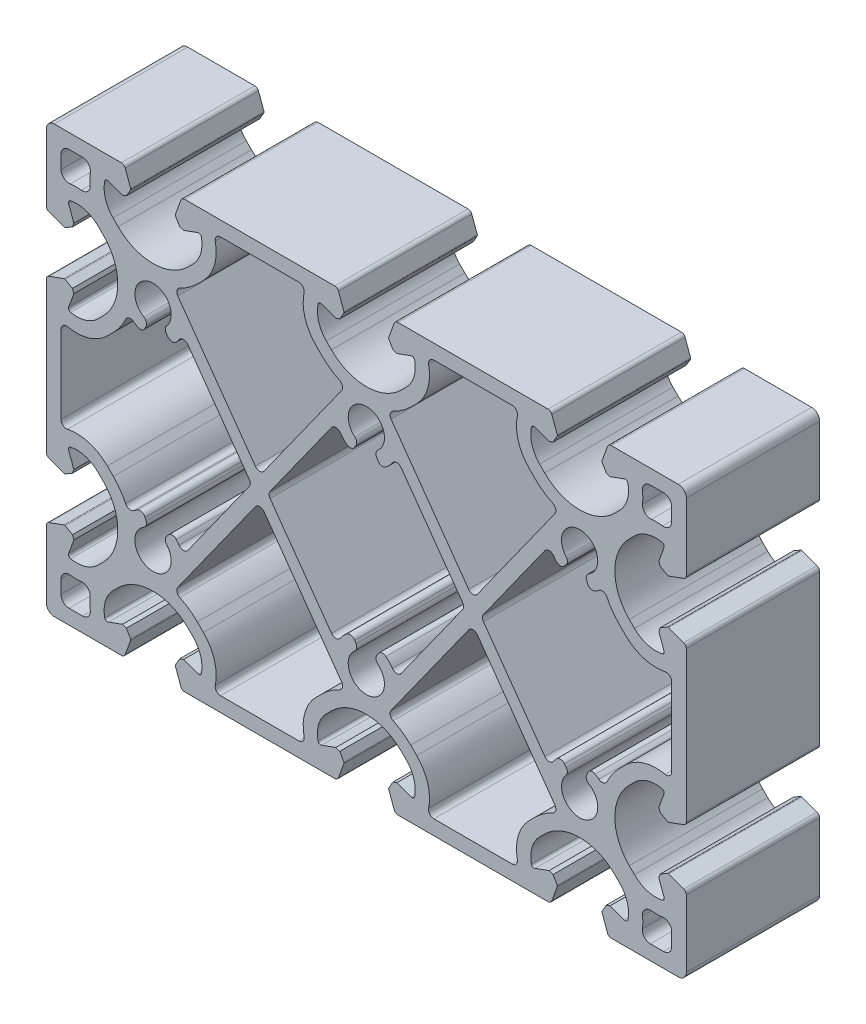
SolidWorks part; units mm, degrees
material "6005-T5"
ref_plane "Front" through (0, 0, 0) normal (0, 0, 1) x (1, 0, 0)
ref_plane "Top" through (0, 0, 0) normal (0, 1, 0) x (1, 0, 0)
ref_plane "Right" through (0, 0, 0) normal (1, 0, 0) x (0, 0, -1)
sketch "Sk Main Extrusion" plane through (0, 0, 0) normal (0, 0, 1) x (1, 0, 0)
  line L30 (-57.25, 35.75) -> (-57.25, 33.2481)
  line L31 (-53.2481, 37.25) -> (-55.75, 37.25)
  line L32 (-30.5557, 28.5773) -> (-31.6915, 27.4415)
  line L33 (-35.3543, 23.6467) -> (-20.8137, 3.2898)
  line L34 (-19.1863, 3.2898) -> (-4.6457, 23.6467)
  line L35 (-8.3085, 27.4415) -> (-9.4443, 28.5773)
  line L36 (-12.653, 37.25) -> (-27.347, 37.25)
  line L37 (-1.934, 16.1059) -> (-2.1871, 15.6675)
  line L38 (-6.5225, 16.7181) -> (-18.0487, 0.5812)
  line L39 (-18.0487, -0.5812) -> (-6.5225, -16.7181)
  line L40 (-2.1871, -15.6675) -> (-1.934, -16.1059)
  line L41 (1.934, -16.1059) -> (2.1871, -15.6675)
  line L42 (6.5225, -16.7181) -> (18.0487, -0.5812)
  line L43 (18.0487, 0.5812) -> (6.5225, 16.7181)
  line L44 (2.1871, 15.6675) -> (1.934, 16.1059)
  line L45 (9.4443, 28.5773) -> (8.3085, 27.4415)
  line L46 (4.6457, 23.6467) -> (19.1863, 3.2898)
  line L47 (20.8137, 3.2898) -> (35.3543, 23.6467)
  line L48 (31.6915, 27.4415) -> (30.5557, 28.5773)
  line L49 (27.347, 37.25) -> (12.653, 37.25)
  line L50 (37.4767, 16.4592) -> (37.1577, 16.0661)
  line L51 (33.4775, 16.7181) -> (21.9513, 0.5812)
  line L52 (21.9513, -0.5812) -> (33.4775, -16.7181)
  line L53 (37.1577, -16.0661) -> (37.4767, -16.4592)
  line L54 (41.2964, -15.8498) -> (41.4773, -15.377)
  line L55 (47.4415, -11.6915) -> (48.5773, -10.5557)
  line L56 (57.25, -7.347) -> (57.25, 7.347)
  line L57 (48.5773, 10.5557) -> (47.4415, 11.6915)
  line L58 (41.4773, 15.377) -> (41.2964, 15.8498)
  line L59 (57.25, 33.2481) -> (57.25, 35.75)
  line L60 (55.75, 37.25) -> (53.2481, 37.25)
  line L61 (-37.1577, 16.0661) -> (-37.4767, 16.4592)
  line L62 (-41.2964, 15.8498) -> (-41.4773, 15.377)
  line L63 (-47.4415, 11.6915) -> (-48.5773, 10.5557)
  line L64 (-57.25, 7.347) -> (-57.25, -7.347)
  line L65 (-48.5773, -10.5557) -> (-47.4415, -11.6915)
  line L66 (-41.4773, -15.377) -> (-41.2964, -15.8498)
  line L67 (-37.4767, -16.4592) -> (-37.1577, -16.0661)
  line L68 (-33.4775, -16.7181) -> (-21.9513, -0.5812)
  line L69 (-21.9513, 0.5812) -> (-33.4775, 16.7181)
  line L70 (-57.25, -33.2481) -> (-57.25, -35.75)
  line L71 (-55.75, -37.25) -> (-53.2481, -37.25)
  line L72 (-4.6457, -23.6467) -> (-19.1863, -3.2898)
  line L73 (-20.8137, -3.2898) -> (-35.3543, -23.6467)
  line L74 (-31.6915, -27.4415) -> (-30.5557, -28.5773)
  line L75 (-27.347, -37.25) -> (-12.653, -37.25)
  line L76 (-9.4443, -28.5773) -> (-8.3085, -27.4415)
  line L77 (8.3085, -27.4415) -> (9.4443, -28.5773)
  line L78 (12.653, -37.25) -> (27.347, -37.25)
  line L79 (30.5557, -28.5773) -> (31.6915, -27.4415)
  line L80 (35.3543, -23.6467) -> (20.8137, -3.2898)
  line L81 (19.1863, -3.2898) -> (4.6457, -23.6467)
  line L82 (57.25, -35.75) -> (57.25, -33.2481)
  line L83 (53.2481, -37.25) -> (55.75, -37.25)
  line L84 (-35.8099, -36.6712) -> (-34.7779, -39.5065)
  line L85 (-34.0732, -40) -> (-5.9268, -40)
  line L86 (-5.2221, -39.5065) -> (-4.1901, -36.6712)
  line L87 (-4.2085, -36.4607) -> (-4.9876, -35.1113)
  line L88 (-4.9876, -35.1113) -> (-5.7185, -34.8453)
  line L89 (-5.7185, -34.8453) -> (-8.3962, -35.8198)
  line L90 (-7.5042, -30.2727) -> (-6.5407, -29.3093)
  line L91 (6.5407, -29.3093) -> (7.5042, -30.2727)
  line L92 (8.3962, -35.8198) -> (5.7185, -34.8453)
  line L93 (5.7185, -34.8453) -> (4.9876, -35.1113)
  line L94 (4.9876, -35.1113) -> (4.2085, -36.4607)
  line L95 (4.1901, -36.6712) -> (5.2221, -39.5065)
  line L96 (5.9268, -40) -> (34.0732, -40)
  line L97 (34.7779, -39.5065) -> (35.8099, -36.6712)
  line L98 (35.7915, -36.4607) -> (35.0124, -35.1113)
  line L99 (35.0124, -35.1113) -> (34.2815, -34.8453)
  line L100 (34.2815, -34.8453) -> (31.6038, -35.8198)
  line L101 (32.4958, -30.2727) -> (33.4593, -29.3093)
  line L102 (46.5407, -29.3093) -> (47.5042, -30.2727)
  line L103 (48.3962, -35.8198) -> (45.7185, -34.8453)
  line L104 (45.7185, -34.8453) -> (44.9876, -35.1113)
  line L105 (44.9876, -35.1113) -> (44.2085, -36.4607)
  line L106 (44.1901, -36.6712) -> (45.2221, -39.5065)
  line L107 (45.9268, -40) -> (58.5, -40)
  line L108 (60, -38.5) -> (60, -25.9268)
  line L109 (59.5065, -25.2221) -> (56.6712, -24.1901)
  line L110 (56.4607, -24.2085) -> (55.1113, -24.9876)
  line L111 (55.1113, -24.9876) -> (54.8453, -25.7185)
  line L112 (54.8453, -25.7185) -> (55.8198, -28.3962)
  line L113 (50.2727, -27.5042) -> (49.3093, -26.5407)
  line L114 (49.3093, -13.4593) -> (50.2727, -12.4958)
  line L115 (55.8198, -11.6038) -> (54.8453, -14.2815)
  line L116 (54.8453, -14.2815) -> (55.1113, -15.0124)
  line L117 (55.1113, -15.0124) -> (56.4607, -15.7915)
  line L118 (56.6712, -15.8099) -> (59.5065, -14.7779)
  line L119 (60, -14.0732) -> (60, 14.0732)
  line L120 (59.5065, 14.7779) -> (56.6712, 15.8099)
  line L121 (56.4607, 15.7915) -> (55.1113, 15.0124)
  line L122 (55.1113, 15.0124) -> (54.8453, 14.2815)
  line L123 (54.8453, 14.2815) -> (55.8198, 11.6038)
  line L124 (50.2727, 12.4958) -> (49.3093, 13.4593)
  line L125 (49.3093, 26.5407) -> (50.2727, 27.5042)
  line L126 (55.8198, 28.3962) -> (54.8453, 25.7185)
  line L127 (54.8453, 25.7185) -> (55.1113, 24.9876)
  line L128 (55.1113, 24.9876) -> (56.4607, 24.2085)
  line L129 (56.6712, 24.1901) -> (59.5065, 25.2221)
  line L130 (60, 25.9268) -> (60, 38.5)
  line L131 (58.5, 40) -> (45.9268, 40)
  line L132 (45.2221, 39.5065) -> (44.1901, 36.6712)
  line L133 (44.2085, 36.4607) -> (44.9876, 35.1113)
  line L134 (44.9876, 35.1113) -> (45.7185, 34.8453)
  line L135 (45.7185, 34.8453) -> (48.3962, 35.8198)
  line L136 (47.5042, 30.2727) -> (46.5407, 29.3093)
  line L137 (33.4593, 29.3093) -> (32.4958, 30.2727)
  line L138 (31.6038, 35.8198) -> (34.2815, 34.8453)
  line L139 (34.2815, 34.8453) -> (35.0124, 35.1113)
  line L140 (35.0124, 35.1113) -> (35.7915, 36.4607)
  line L141 (35.8099, 36.6712) -> (34.7779, 39.5065)
  line L142 (34.0732, 40) -> (5.9268, 40)
  line L143 (5.2221, 39.5065) -> (4.1901, 36.6712)
  line L144 (4.2085, 36.4607) -> (4.9876, 35.1113)
  line L145 (4.9876, 35.1113) -> (5.7185, 34.8453)
  line L146 (5.7185, 34.8453) -> (8.3962, 35.8198)
  line L147 (7.5042, 30.2727) -> (6.5407, 29.3093)
  line L148 (-6.5407, 29.3093) -> (-7.5042, 30.2727)
  line L149 (-8.3962, 35.8198) -> (-5.7185, 34.8453)
  line L150 (-5.7185, 34.8453) -> (-4.9876, 35.1113)
  line L151 (-4.9876, 35.1113) -> (-4.2085, 36.4607)
  line L152 (-4.1901, 36.6712) -> (-5.2221, 39.5065)
  line L153 (-5.9268, 40) -> (-34.0732, 40)
  line L154 (-34.7779, 39.5065) -> (-35.8099, 36.6712)
  line L155 (-35.7915, 36.4607) -> (-35.0124, 35.1113)
  line L156 (-35.0124, 35.1113) -> (-34.2815, 34.8453)
  line L157 (-34.2815, 34.8453) -> (-31.6038, 35.8198)
  line L158 (-32.4958, 30.2727) -> (-33.4593, 29.3093)
  line L159 (-46.5407, 29.3093) -> (-47.5042, 30.2727)
  line L160 (-48.3962, 35.8198) -> (-45.7185, 34.8453)
  line L161 (-45.7185, 34.8453) -> (-44.9876, 35.1113)
  line L162 (-44.9876, 35.1113) -> (-44.2085, 36.4607)
  line L163 (-44.1901, 36.6712) -> (-45.2221, 39.5065)
  line L164 (-45.9268, 40) -> (-58.5, 40)
  line L165 (-60, 38.5) -> (-60, 25.9268)
  line L166 (-59.5065, 25.2221) -> (-56.6712, 24.1901)
  line L167 (-56.4607, 24.2085) -> (-55.1113, 24.9876)
  line L168 (-55.1113, 24.9876) -> (-54.8453, 25.7185)
  line L169 (-54.8453, 25.7185) -> (-55.8198, 28.3962)
  line L170 (-50.2727, 27.5042) -> (-49.3093, 26.5407)
  line L171 (-49.3093, 13.4593) -> (-50.2727, 12.4958)
  line L172 (-55.8198, 11.6038) -> (-54.8453, 14.2815)
  line L173 (-54.8453, 14.2815) -> (-55.1113, 15.0124)
  line L174 (-55.1113, 15.0124) -> (-56.4607, 15.7915)
  line L175 (-56.6712, 15.8099) -> (-59.5065, 14.7779)
  line L176 (-60, 14.0732) -> (-60, -14.0732)
  line L177 (-59.5065, -14.7779) -> (-56.6712, -15.8099)
  line L178 (-56.4607, -15.7915) -> (-55.1113, -15.0124)
  line L179 (-55.1113, -15.0124) -> (-54.8453, -14.2815)
  line L180 (-54.8453, -14.2815) -> (-55.8198, -11.6038)
  line L181 (-50.2727, -12.4958) -> (-49.3093, -13.4593)
  line L182 (-49.3093, -26.5407) -> (-50.2727, -27.5042)
  line L183 (-55.8198, -28.3962) -> (-54.8453, -25.7185)
  line L184 (-54.8453, -25.7185) -> (-55.1113, -24.9876)
  line L185 (-55.1113, -24.9876) -> (-56.4607, -24.2085)
  line L186 (-56.6712, -24.1901) -> (-59.5065, -25.2221)
  line L187 (-60, -25.9268) -> (-60, -38.5)
  line L188 (-58.5, -40) -> (-45.9268, -40)
  line L189 (-45.2221, -39.5065) -> (-44.1901, -36.6712)
  line L190 (-44.2085, -36.4607) -> (-44.9876, -35.1113)
  line L191 (-44.9876, -35.1113) -> (-45.7185, -34.8453)
  line L192 (-45.7185, -34.8453) -> (-48.3962, -35.8198)
  line L193 (-47.5042, -30.2727) -> (-46.5407, -29.3093)
  line L194 (-33.4593, -29.3093) -> (-32.4958, -30.2727)
  line L195 (-31.6038, -35.8198) -> (-34.2815, -34.8453)
  line L196 (-34.2815, -34.8453) -> (-35.0124, -35.1113)
  line L197 (-35.0124, -35.1113) -> (-35.7915, -36.4607)
  line L198 (-17.235, 0) -> (17.235, 0) construction
  line L199 (0, 20) -> (0, -20) construction
  arc A48 (-55.75, 37.25) -> (-57.25, 35.75) centre (-55.75, 35.75) ccw
  arc A49 (-57.25, 33.2481) -> (-55.5375, 31.7633) centre (-55.75, 33.2481) ccw
  arc A50 (-53.4532, 31.794) -> (-55.5375, 31.7633) centre (-54.3755, 23.646) ccw
  arc A51 (-53.4532, 31.794) -> (-51.794, 33.4532) centre (-53.2844, 33.2844) ccw
  arc A52 (-51.7633, 35.5375) -> (-51.794, 33.4532) centre (-43.646, 34.3755) ccw
  arc A53 (-51.7633, 35.5375) -> (-53.2481, 37.25) centre (-53.2481, 35.75) ccw
  arc A54 (-27.347, 37.25) -> (-28.326, 36.0463) centre (-27.347, 36.25) ccw
  arc A55 (-30.5557, 28.5773) -> (-28.326, 36.0463) centre (-36.354, 34.3755) ccw
  arc A56 (-34.9687, 25.1317) -> (-31.6915, 27.4415) centre (-40, 35.75) ccw
  arc A57 (-34.9687, 25.1317) -> (-35.3543, 23.6467) centre (-34.5406, 24.228) ccw
  arc A58 (-20.8137, 3.2898) -> (-19.1863, 3.2898) centre (-20, 3.8711) ccw
  arc A59 (-4.6457, 23.6467) -> (-5.0313, 25.1317) centre (-5.4594, 24.228) ccw
  arc A60 (-8.3085, 27.4415) -> (-5.0313, 25.1317) centre (0, 35.75) ccw
  arc A61 (-11.674, 36.0463) -> (-9.4443, 28.5773) centre (-3.646, 34.3755) ccw
  arc A62 (-11.674, 36.0463) -> (-12.653, 37.25) centre (-12.653, 36.25) ccw
  arc A63 (-1.934, 16.1059) -> (-2.1636, 17.3773) centre (-2.8, 16.6059) ccw
  arc A64 (-3.6762, 15.3853) -> (-2.1871, 15.6675) centre (-3.0531, 16.1675) ccw
  arc A65 (-4.8851, 16.6916) -> (-3.6762, 15.3853) centre (0, 20) ccw
  arc A66 (-4.8851, 16.6916) -> (-6.5225, 16.7181) centre (-5.7131, 16.1308) ccw
  arc A67 (-18.0487, 0.5812) -> (-18.0487, -0.5812) centre (-17.235, 0) ccw
  arc A68 (-6.5225, -16.7181) -> (-4.8851, -16.6916) centre (-5.7131, -16.1308) ccw
  arc A69 (-3.6762, -15.3853) -> (-4.8851, -16.6916) centre (0, -20) ccw
  arc A70 (-2.1871, -15.6675) -> (-3.6762, -15.3853) centre (-3.0531, -16.1675) ccw
  arc A71 (-2.1636, -17.3773) -> (-1.934, -16.1059) centre (-2.8, -16.6059) ccw
  arc A72 (-2.1636, -17.3773) -> (2.1636, -17.3773) centre (0, -20) ccw
  arc A73 (1.934, -16.1059) -> (2.1636, -17.3773) centre (2.8, -16.6059) ccw
  arc A74 (3.6762, -15.3853) -> (2.1871, -15.6675) centre (3.0531, -16.1675) ccw
  arc A75 (4.8851, -16.6916) -> (3.6762, -15.3853) centre (0, -20) ccw
  arc A76 (4.8851, -16.6916) -> (6.5225, -16.7181) centre (5.7131, -16.1308) ccw
  arc A77 (18.0487, -0.5812) -> (18.0487, 0.5812) centre (17.235, 0) ccw
  arc A78 (6.5225, 16.7181) -> (4.8851, 16.6916) centre (5.7131, 16.1308) ccw
  arc A79 (3.6762, 15.3853) -> (4.8851, 16.6916) centre (0, 20) ccw
  arc A80 (2.1871, 15.6675) -> (3.6762, 15.3853) centre (3.0531, 16.1675) ccw
  arc A81 (2.1636, 17.3773) -> (1.934, 16.1059) centre (2.8, 16.6059) ccw
  arc A82 (2.1636, 17.3773) -> (-2.1636, 17.3773) centre (0, 20) ccw
  arc A83 (12.653, 37.25) -> (11.674, 36.0463) centre (12.653, 36.25) ccw
  arc A84 (9.4443, 28.5773) -> (11.674, 36.0463) centre (3.646, 34.3755) ccw
  arc A85 (5.0313, 25.1317) -> (8.3085, 27.4415) centre (0, 35.75) ccw
  arc A86 (5.0313, 25.1317) -> (4.6457, 23.6467) centre (5.4594, 24.228) ccw
  arc A87 (19.1863, 3.2898) -> (20.8137, 3.2898) centre (20, 3.8711) ccw
  arc A88 (35.3543, 23.6467) -> (34.9687, 25.1317) centre (34.5406, 24.228) ccw
  arc A89 (31.6915, 27.4415) -> (34.9687, 25.1317) centre (40, 35.75) ccw
  arc A90 (28.326, 36.0463) -> (30.5557, 28.5773) centre (36.354, 34.3755) ccw
  arc A91 (28.326, 36.0463) -> (27.347, 37.25) centre (27.347, 36.25) ccw
  arc A92 (-34.7779, -39.5065) -> (-34.0732, -40) centre (-34.0732, -39.25) ccw
  arc A93 (-5.9268, -40) -> (-5.2221, -39.5065) centre (-5.9268, -39.25) ccw
  arc A94 (-4.1901, -36.6712) -> (-4.2085, -36.4607) centre (-4.425, -36.5857) ccw
  arc A95 (-9.057, -35.4507) -> (-8.3962, -35.8198) centre (-8.5672, -35.35) ccw
  arc A96 (-7.5042, -30.2727) -> (-9.057, -35.4507) centre (-3.4737, -34.3032) ccw
  arc A97 (6.5407, -29.3093) -> (-6.5407, -29.3093) centre (0, -35.85) ccw
  arc A98 (9.057, -35.4507) -> (7.5042, -30.2727) centre (3.4737, -34.3032) ccw
  arc A99 (8.3962, -35.8198) -> (9.057, -35.4507) centre (8.5672, -35.35) ccw
  arc A100 (4.2085, -36.4607) -> (4.1901, -36.6712) centre (4.425, -36.5857) ccw
  arc A101 (5.2221, -39.5065) -> (5.9268, -40) centre (5.9268, -39.25) ccw
  arc A102 (34.0732, -40) -> (34.7779, -39.5065) centre (34.0732, -39.25) ccw
  arc A103 (35.8099, -36.6712) -> (35.7915, -36.4607) centre (35.575, -36.5857) ccw
  arc A104 (30.943, -35.4507) -> (31.6038, -35.8198) centre (31.4328, -35.35) ccw
  arc A105 (32.4958, -30.2727) -> (30.943, -35.4507) centre (36.5263, -34.3032) ccw
  arc A106 (46.5407, -29.3093) -> (33.4593, -29.3093) centre (40, -35.85) ccw
  arc A107 (49.057, -35.4507) -> (47.5042, -30.2727) centre (43.4737, -34.3032) ccw
  arc A108 (48.3962, -35.8198) -> (49.057, -35.4507) centre (48.5672, -35.35) ccw
  arc A109 (44.2085, -36.4607) -> (44.1901, -36.6712) centre (44.425, -36.5857) ccw
  arc A110 (45.2221, -39.5065) -> (45.9268, -40) centre (45.9268, -39.25) ccw
  arc A111 (58.5, -40) -> (60, -38.5) centre (58.5, -38.5) ccw
  arc A112 (60, -25.9268) -> (59.5065, -25.2221) centre (59.25, -25.9268) ccw
  arc A113 (56.6712, -24.1901) -> (56.4607, -24.2085) centre (56.5857, -24.425) ccw
  arc A114 (55.4507, -29.057) -> (55.8198, -28.3962) centre (55.35, -28.5672) ccw
  arc A115 (50.2727, -27.5042) -> (55.4507, -29.057) centre (54.3032, -23.4737) ccw
  arc A116 (49.3093, -13.4593) -> (49.3093, -26.5407) centre (55.85, -20) ccw
  arc A117 (55.4507, -10.943) -> (50.2727, -12.4958) centre (54.3032, -16.5263) ccw
  arc A118 (55.8198, -11.6038) -> (55.4507, -10.943) centre (55.35, -11.4328) ccw
  arc A119 (56.4607, -15.7915) -> (56.6712, -15.8099) centre (56.5857, -15.575) ccw
  arc A120 (59.5065, -14.7779) -> (60, -14.0732) centre (59.25, -14.0732) ccw
  arc A121 (60, 14.0732) -> (59.5065, 14.7779) centre (59.25, 14.0732) ccw
  arc A122 (56.6712, 15.8099) -> (56.4607, 15.7915) centre (56.5857, 15.575) ccw
  arc A123 (55.4507, 10.943) -> (55.8198, 11.6038) centre (55.35, 11.4328) ccw
  arc A124 (50.2727, 12.4958) -> (55.4507, 10.943) centre (54.3032, 16.5263) ccw
  arc A125 (49.3093, 26.5407) -> (49.3093, 13.4593) centre (55.85, 20) ccw
  arc A126 (55.4507, 29.057) -> (50.2727, 27.5042) centre (54.3032, 23.4737) ccw
  arc A127 (55.8198, 28.3962) -> (55.4507, 29.057) centre (55.35, 28.5672) ccw
  arc A128 (56.4607, 24.2085) -> (56.6712, 24.1901) centre (56.5857, 24.425) ccw
  arc A129 (59.5065, 25.2221) -> (60, 25.9268) centre (59.25, 25.9268) ccw
  arc A130 (60, 38.5) -> (58.5, 40) centre (58.5, 38.5) ccw
  arc A131 (45.9268, 40) -> (45.2221, 39.5065) centre (45.9268, 39.25) ccw
  arc A132 (44.1901, 36.6712) -> (44.2085, 36.4607) centre (44.425, 36.5857) ccw
  arc A133 (49.057, 35.4507) -> (48.3962, 35.8198) centre (48.5672, 35.35) ccw
  arc A134 (47.5042, 30.2727) -> (49.057, 35.4507) centre (43.4737, 34.3032) ccw
  arc A135 (33.4593, 29.3093) -> (46.5407, 29.3093) centre (40, 35.85) ccw
  arc A136 (30.943, 35.4507) -> (32.4958, 30.2727) centre (36.5263, 34.3032) ccw
  arc A137 (31.6038, 35.8198) -> (30.943, 35.4507) centre (31.4328, 35.35) ccw
  arc A138 (35.7915, 36.4607) -> (35.8099, 36.6712) centre (35.575, 36.5857) ccw
  arc A139 (34.7779, 39.5065) -> (34.0732, 40) centre (34.0732, 39.25) ccw
  arc A140 (5.9268, 40) -> (5.2221, 39.5065) centre (5.9268, 39.25) ccw
  arc A141 (4.1901, 36.6712) -> (4.2085, 36.4607) centre (4.425, 36.5857) ccw
  arc A142 (9.057, 35.4507) -> (8.3962, 35.8198) centre (8.5672, 35.35) ccw
  arc A143 (7.5042, 30.2727) -> (9.057, 35.4507) centre (3.4737, 34.3032) ccw
  arc A144 (-6.5407, 29.3093) -> (6.5407, 29.3093) centre (0, 35.85) ccw
  arc A145 (-9.057, 35.4507) -> (-7.5042, 30.2727) centre (-3.4737, 34.3032) ccw
  arc A146 (-8.3962, 35.8198) -> (-9.057, 35.4507) centre (-8.5672, 35.35) ccw
  arc A147 (-4.2085, 36.4607) -> (-4.1901, 36.6712) centre (-4.425, 36.5857) ccw
  arc A148 (-5.2221, 39.5065) -> (-5.9268, 40) centre (-5.9268, 39.25) ccw
  arc A149 (-34.0732, 40) -> (-34.7779, 39.5065) centre (-34.0732, 39.25) ccw
  arc A150 (-35.8099, 36.6712) -> (-35.7915, 36.4607) centre (-35.575, 36.5857) ccw
  arc A151 (-30.943, 35.4507) -> (-31.6038, 35.8198) centre (-31.4328, 35.35) ccw
  arc A152 (-32.4958, 30.2727) -> (-30.943, 35.4507) centre (-36.5263, 34.3032) ccw
  arc A153 (-46.5407, 29.3093) -> (-33.4593, 29.3093) centre (-40, 35.85) ccw
  arc A154 (-49.057, 35.4507) -> (-47.5042, 30.2727) centre (-43.4737, 34.3032) ccw
  arc A155 (-48.3962, 35.8198) -> (-49.057, 35.4507) centre (-48.5672, 35.35) ccw
  arc A156 (-44.2085, 36.4607) -> (-44.1901, 36.6712) centre (-44.425, 36.5857) ccw
  arc A157 (-45.2221, 39.5065) -> (-45.9268, 40) centre (-45.9268, 39.25) ccw
  arc A158 (-58.5, 40) -> (-60, 38.5) centre (-58.5, 38.5) ccw
  arc A159 (-60, 25.9268) -> (-59.5065, 25.2221) centre (-59.25, 25.9268) ccw
  arc A160 (-56.6712, 24.1901) -> (-56.4607, 24.2085) centre (-56.5857, 24.425) ccw
  arc A161 (-55.4507, 29.057) -> (-55.8198, 28.3962) centre (-55.35, 28.5672) ccw
  arc A162 (-50.2727, 27.5042) -> (-55.4507, 29.057) centre (-54.3032, 23.4737) ccw
  arc A163 (-49.3093, 13.4593) -> (-49.3093, 26.5407) centre (-55.85, 20) ccw
  arc A164 (-55.4507, 10.943) -> (-50.2727, 12.4958) centre (-54.3032, 16.5263) ccw
  arc A165 (-55.8198, 11.6038) -> (-55.4507, 10.943) centre (-55.35, 11.4328) ccw
  arc A166 (-56.4607, 15.7915) -> (-56.6712, 15.8099) centre (-56.5857, 15.575) ccw
  arc A167 (-59.5065, 14.7779) -> (-60, 14.0732) centre (-59.25, 14.0732) ccw
  arc A168 (-60, -14.0732) -> (-59.5065, -14.7779) centre (-59.25, -14.0732) ccw
  arc A169 (-56.6712, -15.8099) -> (-56.4607, -15.7915) centre (-56.5857, -15.575) ccw
  arc A170 (-55.4507, -10.943) -> (-55.8198, -11.6038) centre (-55.35, -11.4328) ccw
  arc A171 (-50.2727, -12.4958) -> (-55.4507, -10.943) centre (-54.3032, -16.5263) ccw
  arc A172 (-49.3093, -26.5407) -> (-49.3093, -13.4593) centre (-55.85, -20) ccw
  arc A173 (-55.4507, -29.057) -> (-50.2727, -27.5042) centre (-54.3032, -23.4737) ccw
  arc A174 (-55.8198, -28.3962) -> (-55.4507, -29.057) centre (-55.35, -28.5672) ccw
  arc A175 (-56.4607, -24.2085) -> (-56.6712, -24.1901) centre (-56.5857, -24.425) ccw
  arc A176 (-59.5065, -25.2221) -> (-60, -25.9268) centre (-59.25, -25.9268) ccw
  arc A177 (-60, -38.5) -> (-58.5, -40) centre (-58.5, -38.5) ccw
  arc A178 (-45.9268, -40) -> (-45.2221, -39.5065) centre (-45.9268, -39.25) ccw
  arc A179 (-44.1901, -36.6712) -> (-44.2085, -36.4607) centre (-44.425, -36.5857) ccw
  arc A180 (-49.057, -35.4507) -> (-48.3962, -35.8198) centre (-48.5672, -35.35) ccw
  arc A181 (-47.5042, -30.2727) -> (-49.057, -35.4507) centre (-43.4737, -34.3032) ccw
  arc A182 (-33.4593, -29.3093) -> (-46.5407, -29.3093) centre (-40, -35.85) ccw
  arc A183 (-30.943, -35.4507) -> (-32.4958, -30.2727) centre (-36.5263, -34.3032) ccw
  arc A184 (-31.6038, -35.8198) -> (-30.943, -35.4507) centre (-31.4328, -35.35) ccw
  arc A185 (-35.7915, -36.4607) -> (-35.8099, -36.6712) centre (-35.575, -36.5857) ccw
  arc A186 (37.4767, 16.4592) -> (37.4502, 17.7509) centre (36.7003, 17.0894) ccw
  arc A187 (35.6427, 16.022) -> (37.1577, 16.0661) centre (36.3812, 16.6963) ccw
  arc A188 (35.1149, 16.6916) -> (35.6427, 16.022) centre (40, 20) ccw
  arc A189 (35.1149, 16.6916) -> (33.4775, 16.7181) centre (34.2869, 16.1308) ccw
  arc A190 (21.9513, 0.5812) -> (21.9513, -0.5812) centre (22.765, 0) ccw
  arc A191 (33.4775, -16.7181) -> (35.1149, -16.6916) centre (34.2869, -16.1308) ccw
  arc A192 (35.6427, -16.022) -> (35.1149, -16.6916) centre (40, -20) ccw
  arc A193 (37.1577, -16.0661) -> (35.6427, -16.022) centre (36.3812, -16.6963) ccw
  arc A194 (37.4502, -17.7509) -> (37.4767, -16.4592) centre (36.7003, -17.0894) ccw
  arc A195 (37.4502, -17.7509) -> (41.7235, -17.0692) centre (40, -20) ccw
  arc A196 (41.2964, -15.8498) -> (41.7235, -17.0692) centre (42.2304, -16.2072) ccw
  arc A197 (42.9034, -14.8638) -> (41.4773, -15.377) centre (42.4113, -15.7343) ccw
  arc A198 (43.6133, -15.3359) -> (42.9034, -14.8638) centre (40, -20) ccw
  arc A199 (43.6133, -15.3359) -> (45.1296, -14.9732) centre (44.2257, -14.5453) ccw
  arc A200 (47.4415, -11.6915) -> (45.1296, -14.9732) centre (55.75, -20) ccw
  arc A201 (56.0463, -8.326) -> (48.5773, -10.5557) centre (54.3755, -16.354) ccw
  arc A202 (56.0463, -8.326) -> (57.25, -7.347) centre (56.25, -7.347) ccw
  arc A203 (57.25, 7.347) -> (56.0463, 8.326) centre (56.25, 7.347) ccw
  arc A204 (48.5773, 10.5557) -> (56.0463, 8.326) centre (54.3755, 16.354) ccw
  arc A205 (45.1296, 14.9732) -> (47.4415, 11.6915) centre (55.75, 20) ccw
  arc A206 (45.1296, 14.9732) -> (43.6133, 15.3359) centre (44.2257, 14.5453) ccw
  arc A207 (42.9034, 14.8638) -> (43.6133, 15.3359) centre (40, 20) ccw
  arc A208 (41.4773, 15.377) -> (42.9034, 14.8638) centre (42.4113, 15.7343) ccw
  arc A209 (41.7235, 17.0692) -> (41.2964, 15.8498) centre (42.2304, 16.2072) ccw
  arc A210 (41.7235, 17.0692) -> (37.4502, 17.7509) centre (40, 20) ccw
  arc A211 (57.25, 35.75) -> (55.75, 37.25) centre (55.75, 35.75) ccw
  arc A212 (53.2481, 37.25) -> (51.7633, 35.5375) centre (53.2481, 35.75) ccw
  arc A213 (51.794, 33.4532) -> (51.7633, 35.5375) centre (43.646, 34.3755) ccw
  arc A214 (51.794, 33.4532) -> (53.4532, 31.794) centre (53.2844, 33.2844) ccw
  arc A215 (55.5375, 31.7633) -> (53.4532, 31.794) centre (54.3755, 23.646) ccw
  arc A216 (55.5375, 31.7633) -> (57.25, 33.2481) centre (55.75, 33.2481) ccw
  arc A217 (-33.4775, 16.7181) -> (-35.1149, 16.6916) centre (-34.2869, 16.1308) ccw
  arc A218 (-35.6427, 16.022) -> (-35.1149, 16.6916) centre (-40, 20) ccw
  arc A219 (-37.1577, 16.0661) -> (-35.6427, 16.022) centre (-36.3812, 16.6963) ccw
  arc A220 (-37.4502, 17.7509) -> (-37.4767, 16.4592) centre (-36.7003, 17.0894) ccw
  arc A221 (-37.4502, 17.7509) -> (-41.7235, 17.0692) centre (-40, 20) ccw
  arc A222 (-41.2964, 15.8498) -> (-41.7235, 17.0692) centre (-42.2304, 16.2072) ccw
  arc A223 (-42.9034, 14.8638) -> (-41.4773, 15.377) centre (-42.4113, 15.7343) ccw
  arc A224 (-43.6133, 15.3359) -> (-42.9034, 14.8638) centre (-40, 20) ccw
  arc A225 (-43.6133, 15.3359) -> (-45.1296, 14.9732) centre (-44.2257, 14.5453) ccw
  arc A226 (-47.4415, 11.6915) -> (-45.1296, 14.9732) centre (-55.75, 20) ccw
  arc A227 (-56.0463, 8.326) -> (-48.5773, 10.5557) centre (-54.3755, 16.354) ccw
  arc A228 (-56.0463, 8.326) -> (-57.25, 7.347) centre (-56.25, 7.347) ccw
  arc A229 (-57.25, -7.347) -> (-56.0463, -8.326) centre (-56.25, -7.347) ccw
  arc A230 (-48.5773, -10.5557) -> (-56.0463, -8.326) centre (-54.3755, -16.354) ccw
  arc A231 (-45.1296, -14.9732) -> (-47.4415, -11.6915) centre (-55.75, -20) ccw
  arc A232 (-45.1296, -14.9732) -> (-43.6133, -15.3359) centre (-44.2257, -14.5453) ccw
  arc A233 (-42.9034, -14.8638) -> (-43.6133, -15.3359) centre (-40, -20) ccw
  arc A234 (-41.4773, -15.377) -> (-42.9034, -14.8638) centre (-42.4113, -15.7343) ccw
  arc A235 (-41.7235, -17.0692) -> (-41.2964, -15.8498) centre (-42.2304, -16.2072) ccw
  arc A236 (-41.7235, -17.0692) -> (-37.4502, -17.7509) centre (-40, -20) ccw
  arc A237 (-37.4767, -16.4592) -> (-37.4502, -17.7509) centre (-36.7003, -17.0894) ccw
  arc A238 (-35.6427, -16.022) -> (-37.1577, -16.0661) centre (-36.3812, -16.6963) ccw
  arc A239 (-35.1149, -16.6916) -> (-35.6427, -16.022) centre (-40, -20) ccw
  arc A240 (-35.1149, -16.6916) -> (-33.4775, -16.7181) centre (-34.2869, -16.1308) ccw
  arc A241 (-21.9513, -0.5812) -> (-21.9513, 0.5812) centre (-22.765, 0) ccw
  arc A242 (-53.2481, -37.25) -> (-51.7633, -35.5375) centre (-53.2481, -35.75) ccw
  arc A243 (-51.794, -33.4532) -> (-51.7633, -35.5375) centre (-43.646, -34.3755) ccw
  arc A244 (-51.794, -33.4532) -> (-53.4532, -31.794) centre (-53.2844, -33.2844) ccw
  arc A245 (-55.5375, -31.7633) -> (-53.4532, -31.794) centre (-54.3755, -23.646) ccw
  arc A246 (-55.5375, -31.7633) -> (-57.25, -33.2481) centre (-55.75, -33.2481) ccw
  arc A247 (-57.25, -35.75) -> (-55.75, -37.25) centre (-55.75, -35.75) ccw
  arc A248 (-5.0313, -25.1317) -> (-4.6457, -23.6467) centre (-5.4594, -24.228) ccw
  arc A249 (-19.1863, -3.2898) -> (-20.8137, -3.2898) centre (-20, -3.8711) ccw
  arc A250 (-35.3543, -23.6467) -> (-34.9687, -25.1317) centre (-34.5406, -24.228) ccw
  arc A251 (-31.6915, -27.4415) -> (-34.9687, -25.1317) centre (-40, -35.75) ccw
  arc A252 (-28.326, -36.0463) -> (-30.5557, -28.5773) centre (-36.354, -34.3755) ccw
  arc A253 (-28.326, -36.0463) -> (-27.347, -37.25) centre (-27.347, -36.25) ccw
  arc A254 (-12.653, -37.25) -> (-11.674, -36.0463) centre (-12.653, -36.25) ccw
  arc A255 (-9.4443, -28.5773) -> (-11.674, -36.0463) centre (-3.646, -34.3755) ccw
  arc A256 (-5.0313, -25.1317) -> (-8.3085, -27.4415) centre (0, -35.75) ccw
  arc A257 (11.674, -36.0463) -> (9.4443, -28.5773) centre (3.646, -34.3755) ccw
  arc A258 (11.674, -36.0463) -> (12.653, -37.25) centre (12.653, -36.25) ccw
  arc A259 (27.347, -37.25) -> (28.326, -36.0463) centre (27.347, -36.25) ccw
  arc A260 (30.5557, -28.5773) -> (28.326, -36.0463) centre (36.354, -34.3755) ccw
  arc A261 (34.9687, -25.1317) -> (31.6915, -27.4415) centre (40, -35.75) ccw
  arc A262 (34.9687, -25.1317) -> (35.3543, -23.6467) centre (34.5406, -24.228) ccw
  arc A263 (20.8137, -3.2898) -> (19.1863, -3.2898) centre (20, -3.8711) ccw
  arc A264 (4.6457, -23.6467) -> (5.0313, -25.1317) centre (5.4594, -24.228) ccw
  arc A265 (8.3085, -27.4415) -> (5.0313, -25.1317) centre (0, -35.75) ccw
  arc A266 (55.75, -37.25) -> (57.25, -35.75) centre (55.75, -35.75) ccw
  arc A267 (57.25, -33.2481) -> (55.5375, -31.7633) centre (55.75, -33.2481) ccw
  arc A268 (53.4532, -31.794) -> (55.5375, -31.7633) centre (54.3755, -23.646) ccw
  arc A269 (53.4532, -31.794) -> (51.794, -33.4532) centre (53.2844, -33.2844) ccw
  arc A270 (51.7633, -35.5375) -> (51.794, -33.4532) centre (43.646, -34.3755) ccw
  arc A271 (51.7633, -35.5375) -> (53.2481, -37.25) centre (53.2481, -35.75) ccw
  point P617 (0, 0)
extrude "Main Extrusion" add sketch "Sk Main Extrusion" against normal blind 25
sketch "Threaded Insert Mate Sketch" plane through (0, 0, 0) normal (0, 0, 1) x (1, 0, 0)
  line L1 (5.9268, -40) -> (34.0732, -40) construction
  line L2 (-57.25, 0) -> (57.25, 0) construction
  line L3 (-57.25, 7.347) -> (-57.25, -7.347) construction
  line L4 (57.25, -7.347) -> (57.25, 7.347) construction
  line L5 (-20, 37.25) -> (-20, -37.25) construction
  line L6 (-12.653, 37.25) -> (-27.347, 37.25) construction
  line L7 (-27.347, -37.25) -> (-12.653, -37.25) construction
  line L8 (20, 37.25) -> (20, -37.25) construction
  line L9 (27.347, 37.25) -> (12.653, 37.25) construction
  line L10 (12.653, -37.25) -> (27.347, -37.25) construction
  line L11 (-56.8107, -36.8107) -> (-52.2238, -32.2238) construction
  line L12 (0, 23.4) -> (0, -23.4) construction
  circle A0 centre (0, -32.7) radius 5.6515
  circle A1 centre (-40, -32.7) radius 5.6515
  arc A2 (-57.25, -35.75) -> (-55.75, -37.25) centre (-55.75, -35.75) ccw construction
  arc A3 (-51.794, -33.4532) -> (-53.4532, -31.794) centre (-53.2844, -33.2844) ccw construction
  circle A4 centre (-52.7, -20) radius 5.6515
  arc A5 (2.1636, 17.3773) -> (-2.1636, 17.3773) centre (0, 20) ccw construction
  arc A6 (-2.1636, -17.3773) -> (2.1636, -17.3773) centre (0, -20) ccw construction
  circle A7 centre (52.7, -20) radius 5.6515
  circle A8 centre (40, -32.7) radius 5.6515
  circle A9 centre (52.7, 20) radius 5.6515
  circle A10 centre (40, 32.7) radius 5.6515
  circle A11 centre (0, 32.7) radius 5.6515
  circle A12 centre (-40, 32.7) radius 5.6515
  circle A13 centre (-52.7, 20) radius 5.6515
  dimension "D2" = 11.303
  dimension "D1" = 7.3
equation "\"Weight kg\"= round ( \"SW-Mass\" , 2 )"
equation "\"Weight lbs\"= round ( \"SW-Mass\" * 2.2046 , 2 )"
equation "\"Length mm\"= round ( \"Length@Main Extrusion\" , 2 )"
equation "\"Length in\"= round ( \"Length@Main Extrusion\" / 25.4 , 3 )"
